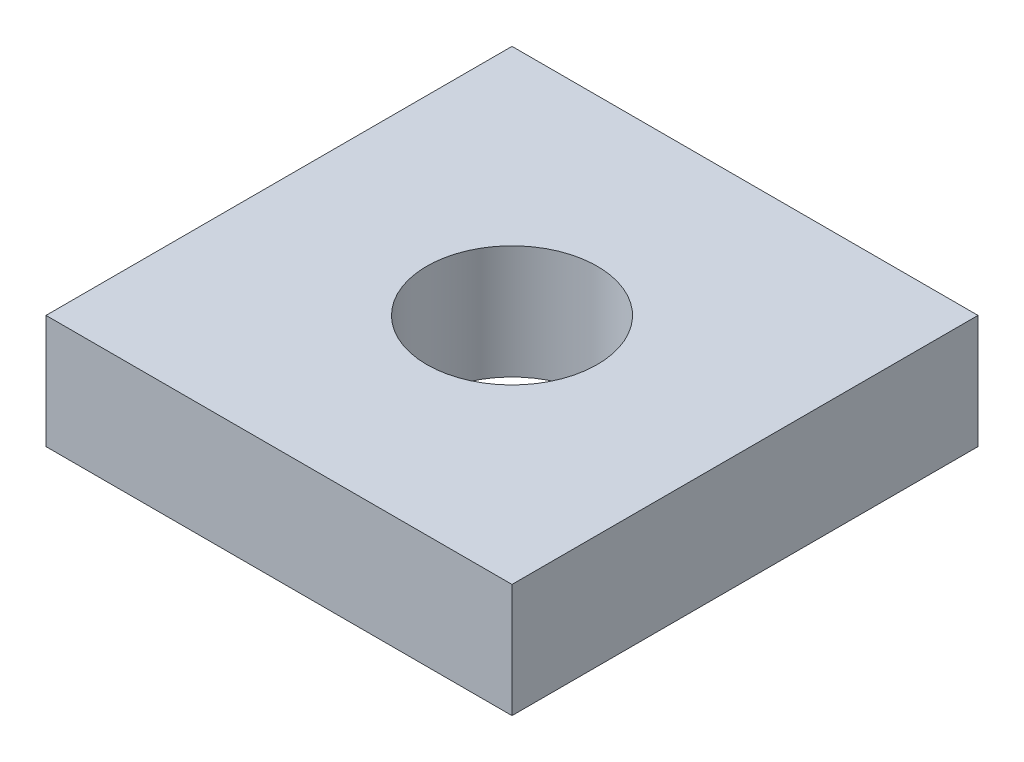
SolidWorks part; units mm, degrees
ref_plane "Спереди" through (0, 0, 0) normal (0, 0, 1) x (1, 0, 0)
ref_plane "Сверху" through (0, 0, 0) normal (0, 1, 0) x (1, 0, 0)
ref_plane "Справа" through (0, 0, 0) normal (1, 0, 0) x (0, 0, -1)
sketch "Эскиз1" plane through (0, 0, 0) normal (0, 1, 0) x (1, 0, 0)
  line L0 (4.1, 8.2) -> (4.1, 0) construction
  line L1 (0, 0) -> (8.2, 0)
  line L2 (0, 0) -> (0, 8.2)
  line L3 (0, 8.2) -> (8.2, 8.2)
  line L4 (8.2, 0) -> (8.2, 8.2)
  line L5 (0, 4.1) -> (4.1, 4.1) construction
  circle A0 centre (4.1, 4.1) radius 1.5
  dimension "D3" = 3
  dimension "D1" = 8.2
  dimension "D2" = 8.2
extrude "Бобышка-Вытянуть1" add sketch "Эскиз1" along normal blind 2
